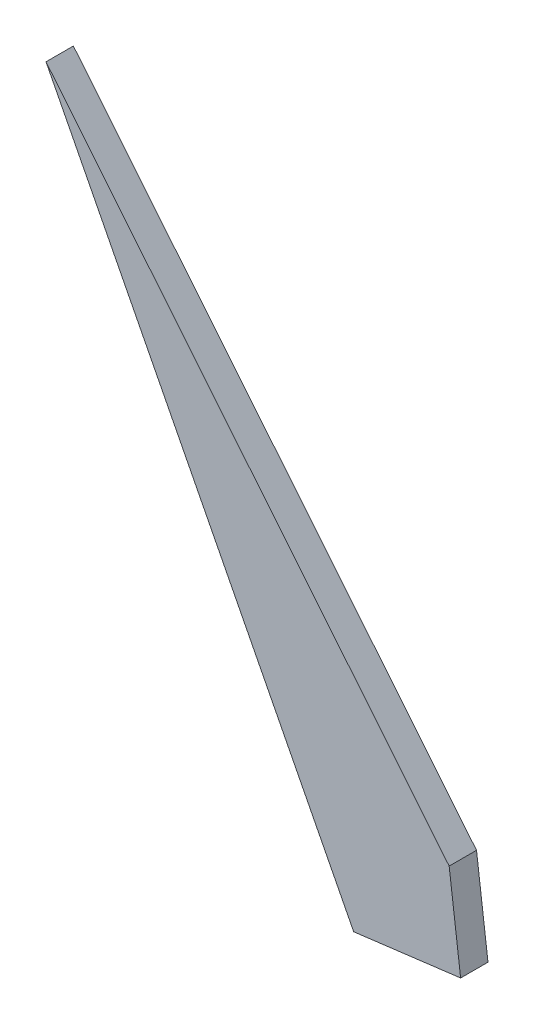
SolidWorks part; units mm, degrees
ref_plane "Plan de face" through (0, 0, 0) normal (0, 0, 1) x (1, 0, 0)
ref_plane "Plan de dessus" through (0, 0, 0) normal (0, 1, 0) x (1, 0, 0)
ref_plane "Plan de droite" through (0, 0, 0) normal (1, 0, 0) x (0, 0, -1)
sketch "Esquisse1" plane through (0, 0, 0) normal (0, 0, 1) x (1, 0, 0)
  line L0 (-2.8693, -1.2277) -> (-47.0775, 53.0461)
  line L1 (-47.0775, 53.0461) -> (-13.3396, -12.7017)
  line L4 (-2.8693, -1.2277) -> (-1.6123, -11.2277)
  line L5 (-1.6123, -11.2277) -> (-13.3396, -12.7017)
  line L6 (-2.0612, -7.6564) -> (-2.9766, -0.3741) construction
  line L7 (-35.7924, 39.1915) -> (-64.2396, 74.1157) construction
  line L8 (-2.326, -1.8946) -> (-35.7924, 39.1915) construction
  point P3 (-1.4825, -10.9978)
  point P4 (-13.7316, -6.6602)
  point P5 (-48.8683, 52.4837)
  point P6 (0, 0)
  point P7 (-21.3194, -1.8946)
  point P8 (-26.1908, -12.1491)
  point P9 (-60.6157, 69.6667)
  point P11 (-7.6601, -10.9978)
  point P12 (-52.6305, 59.8634)
  point P15 (0, 0)
  point P16 (-0.9661, -12.7154)
  point P17 (-6.5315, -13.1071)
  point P18 (-6.3611, -13.2829)
  point P19 (0, 0)
  point P20 (-2.4327, -3.6128)
  point P23 (-3.2947, -0.8549)
  point P24 (0, 0)
  point P25 (-3.8404, -0.1951)
  point P28 (-2.6604, -1.4842)
  point P29 (0, 0)
  point P30 (-21.9521, -1.2277)
  point P31 (-12.1694, -7.1805)
  point P32 (-2.8598, -1.2393)
  point P33 (0, 0)
  point P34 (-1.6092, -11.2523)
  point P35 (-2.0426, -10.1778)
  point P36 (-28.0645, 5.186)
  point P37 (-6.5403, -10.7816)
  point P38 (0, 0)
  point P39 (0, 0)
  point P41 (-10.3034, -11.7527)
  point P43 (0, 0)
  point P44 (0, 0)
  dimension "D1" = 10
  dimension "D2" = 110
  dimension "D3" = 70
extrude "Boss.-Extru.1" add sketch "Esquisse1" along normal blind 3
